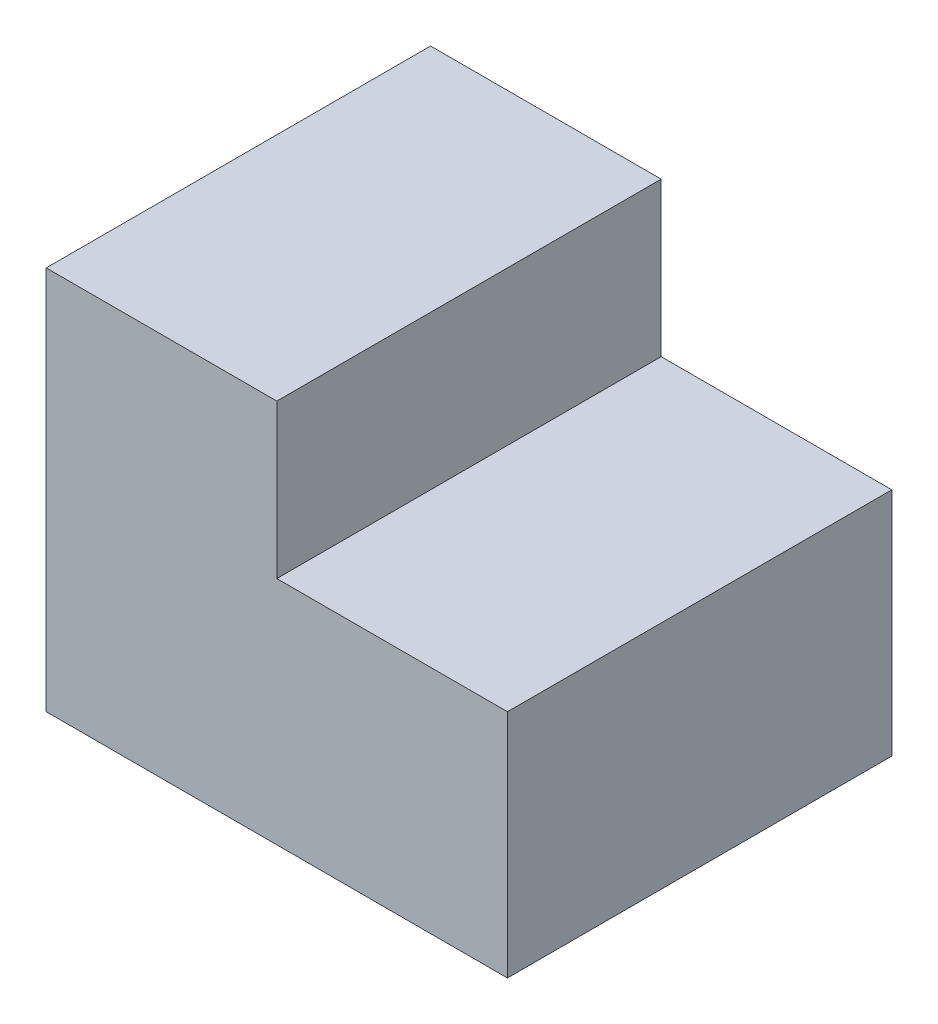
SolidWorks part; units mm, degrees
ref_plane "Front Plane" through (0, 0, 0) normal (0, 0, 1) x (1, 0, 0)
ref_plane "Top Plane" through (0, 0, 0) normal (0, 1, 0) x (1, 0, 0)
ref_plane "Right Plane" through (0, 0, 0) normal (1, 0, 0) x (0, 0, -1)
sketch "Sketch1" plane through (0, 0, 0) normal (0, 0, 1) x (1, 0, 0)
  line L0 (-30, 25) -> (-15, 25)
  line L1 (-15, 25) -> (-15, 15)
  line L2 (-15, 15) -> (0, 15)
  line L3 (0, 15) -> (0, 0)
  line L4 (0, 0) -> (-30, 0)
  line L5 (-30, 0) -> (-30, 25)
  dimension "D1" = 15
  dimension "D2" = 10
  dimension "D3" = 25
  dimension "D4" = 15
extrude "Boss-Extrude1" add sketch "Sketch1" along normal blind 25
